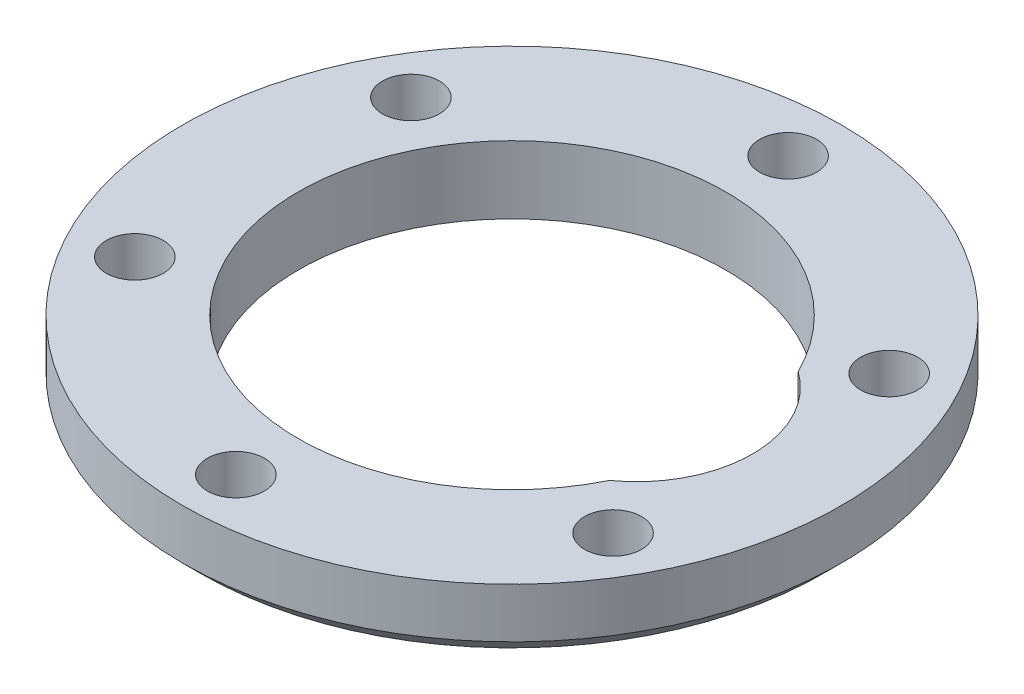
SolidWorks part; units mm, degrees
material "PET"
ref_plane "Спереди" through (0, 0, 0) normal (0, 0, 1) x (1, 0, 0)
ref_plane "Сверху" through (0, 0, 0) normal (0, 1, 0) x (1, 0, 0)
ref_plane "Справа" through (0, 0, 0) normal (1, 0, 0) x (0, 0, -1)
sketch "Эскиз1" plane through (0, 0, 0) normal (0, 1, 0) x (1, 0, 0)
  line L0 (0, 0) -> (0, -26.8765) construction
  circle A0 centre (0, 0) radius 18.5
  circle A1 centre (-13.4234, -7.75) radius 1.6
  circle A2 centre (0, -15.5) radius 1.6
  circle A3 centre (-13.4234, 7.75) radius 1.6
  circle A4 centre (0, 15.5) radius 1.6
  circle A5 centre (13.4234, 7.75) radius 1.6
  circle A6 centre (13.4234, -7.75) radius 1.6
  arc A7 (10.7679, -5.2965) -> (10.7679, 5.2965) centre (7, 0) ccw
  arc A10 (10.7679, 5.2965) -> (10.7679, -5.2965) centre (0, 0) ccw
  point P18 (0, 0)
  dimension "D1" = 37
  dimension "D3" = 3.2
  dimension "D4" = 31
  dimension "D5" = 13
  dimension "D7" = 24
  dimension "D2" = 6
  dimension "D6" = 7
extrude "Бобышка-Вытянуть1" add sketch "Эскиз1" along normal blind 3.8
chamfer "Фаска1" distance 1 angle 45 1 edges at (0, 0, 18.5)
